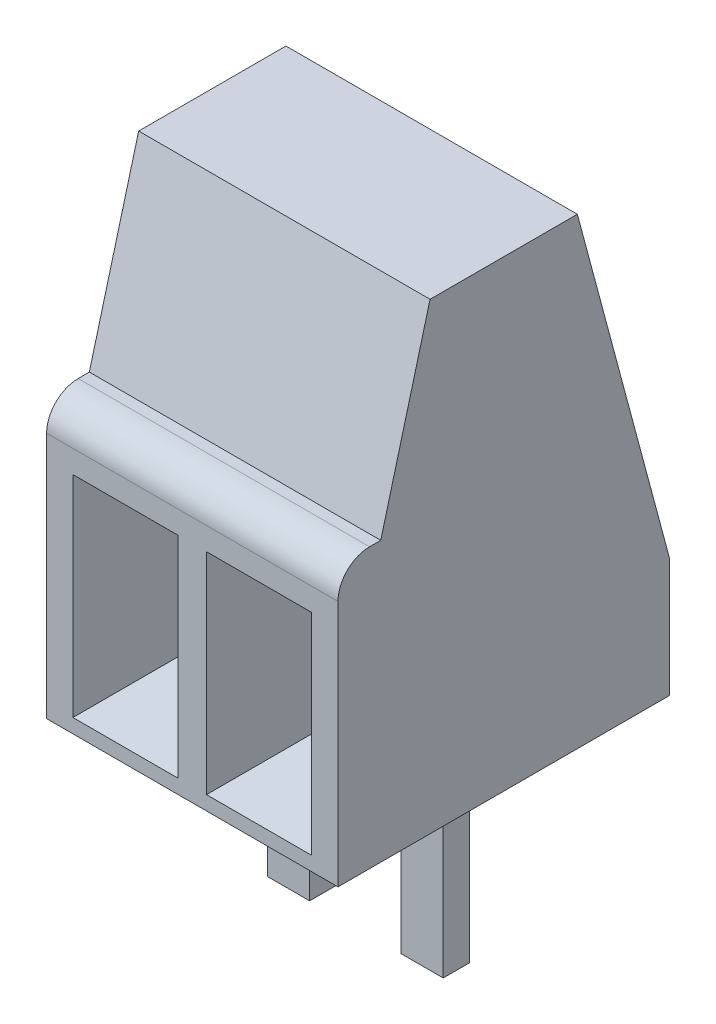
SolidWorks part; units mm, degrees
ref_plane "Front Plane" through (0, 0, 0) normal (0, 0, 1) x (1, 0, 0)
ref_plane "Top Plane" through (0, 0, 0) normal (0, 1, 0) x (1, 0, 0)
ref_plane "Right Plane" through (0, 0, 0) normal (1, 0, 0) x (0, 0, -1)
sketch "Sketch1" plane through (0, 0, 0) normal (0, 1, 0) x (1, 0, 0)
  line L1 (-2.77, -3.15) -> (2.77, -3.15)
  line L2 (-2.77, -3.15) -> (-2.77, 3.15)
  line L3 (-2.77, 3.15) -> (2.77, 3.15)
  line L4 (2.77, -3.15) -> (2.77, 3.15)
  line L5 (-2.77, -3.15) -> (2.77, 3.15) construction
  line L6 (-2.77, 3.15) -> (2.77, -3.15) construction
  point P0 (0, 0)
  dimension "D1" = 5.54
  dimension "D2" = 6.3
extrude "Boss-Extrude1" add sketch "Sketch1" along normal blind 8.8
sketch "Sketch2" plane through (0, 0, 0) normal (0, 1, 0) x (1, 0, 0)
  line L1 (0.87, -0.05) -> (1.67, -0.05)
  line L2 (0.87, -0.05) -> (0.87, 0.45)
  line L3 (0.87, 0.45) -> (1.67, 0.45)
  line L4 (1.67, -0.05) -> (1.67, 0.45)
  line L5 (0.87, -0.05) -> (1.67, 0.45) construction
  line L6 (0.87, 0.45) -> (1.67, -0.05) construction
  line L11 (2.77, 3.15) -> (-2.77, 3.15) construction
  line L13 (-0.87, -0.05) -> (-1.67, -0.05)
  line L14 (-0.87, -0.05) -> (-0.87, 0.45)
  line L15 (-0.87, 0.45) -> (-1.67, 0.45)
  line L16 (-1.67, -0.05) -> (-1.67, 0.45)
  line L17 (-0.87, -0.05) -> (-1.67, 0.45) construction
  line L18 (-0.87, 0.45) -> (-1.67, -0.05) construction
  point P0 (1.27, 0.2)
  point P11 (-1.27, 0.2)
  point P20 (1.27, 0.2)
  dimension "D1" = 2.54
  dimension "D2" = 0.8
  dimension "D3" = 2.95
  dimension "D4" = 0.5
  dimension "D5" = 1.27
extrude "Boss-Extrude2" add sketch "Sketch2" against normal blind 3.6
sketch "Sketch3" plane through (2.77, 0, 0) normal (1, 0, 0) x (0, 0, -1)
  line L1 (-3.15, 8.8) -> (-3.15, 0) construction
  line L2 (-2.55, 5.3) -> (-2.3378, 5.3)
  line L3 (-2.3378, 5.3) -> (-1.4, 8.8)
  line L4 (-3.15, 8.8) -> (3.15, 8.8) construction
  line L5 (-1.4, 8.8) -> (1.4, 8.8)
  line L6 (1.4, 8.8) -> (3.15, 2.2689)
  line L7 (3.15, 8.8) -> (3.15, 0) construction
  line L10 (1.4, 8.8) -> (3.15, 8.8)
  line L11 (3.15, 8.8) -> (3.15, 2.2689)
  line L12 (-3.15, 4.7) -> (-3.15, 8.8)
  line L13 (-3.15, 8.8) -> (-1.4, 8.8)
  line L14 (-3.15, 0) -> (3.15, 0) construction
  arc A0 (-3.15, 4.7) -> (-2.55, 5.3) centre (-2.55, 4.7) cw
  point P18 (0, 8.8)
  line M12 (3.15, 0) -> (3.15, 8.8)
  line M13 (3.15, 8.8) -> (-3.15, 8.8)
  line M14 (-3.15, 8.8) -> (-3.15, 0)
  dimension "D3" = 4.7
  dimension "D1" = 15
  dimension "D2" = 75
  dimension "D4" = 2.8
  dimension "D5" = 5.3
extrude "Cut-Extrude1" cut sketch "Sketch3" against normal up to next contours A0 L2 L3 M14 M13 | L6 M13 M12
sketch "Sketch4" plane through (0, 0, 3.15) normal (0, 0, 1) x (1, 0, 0)
  line L7 (-2.27, 0.2689) -> (-0.27, 0.2689)
  line L8 (-2.27, 0.2689) -> (-2.27, 4.2689)
  line L9 (-2.27, 4.2689) -> (-0.27, 4.2689)
  line L10 (-0.27, 0.2689) -> (-0.27, 4.2689)
  line L11 (-2.27, 0.2689) -> (-0.27, 4.2689) construction
  line L12 (-2.27, 4.2689) -> (-0.27, 0.2689) construction
  line L13 (2.27, 4.2689) -> (0.27, 4.2689)
  line L14 (2.27, 4.2689) -> (2.27, 0.2689)
  line L15 (2.27, 0.2689) -> (0.27, 0.2689)
  line L16 (0.27, 4.2689) -> (0.27, 0.2689)
  line L17 (2.27, 4.2689) -> (0.27, 0.2689) construction
  line L18 (2.27, 0.2689) -> (0.27, 4.2689) construction
  line L29 (0.87, -3.6) -> (1.67, -3.6) construction
  line L30 (-1.67, -3.6) -> (-0.87, -3.6) construction
  point P0 (0, 0)
  point P5 (-1.27, 2.2689)
  point P10 (1.27, 2.2689)
  point P21 (0, 2.2689)
  point P32 (1.27, -3.6)
  point P35 (-1.27, -3.6)
  dimension "D1" = 2
  dimension "D2" = 4
extrude "Cut-Extrude2" cut sketch "Sketch4" against normal blind 3.15 draft 10
